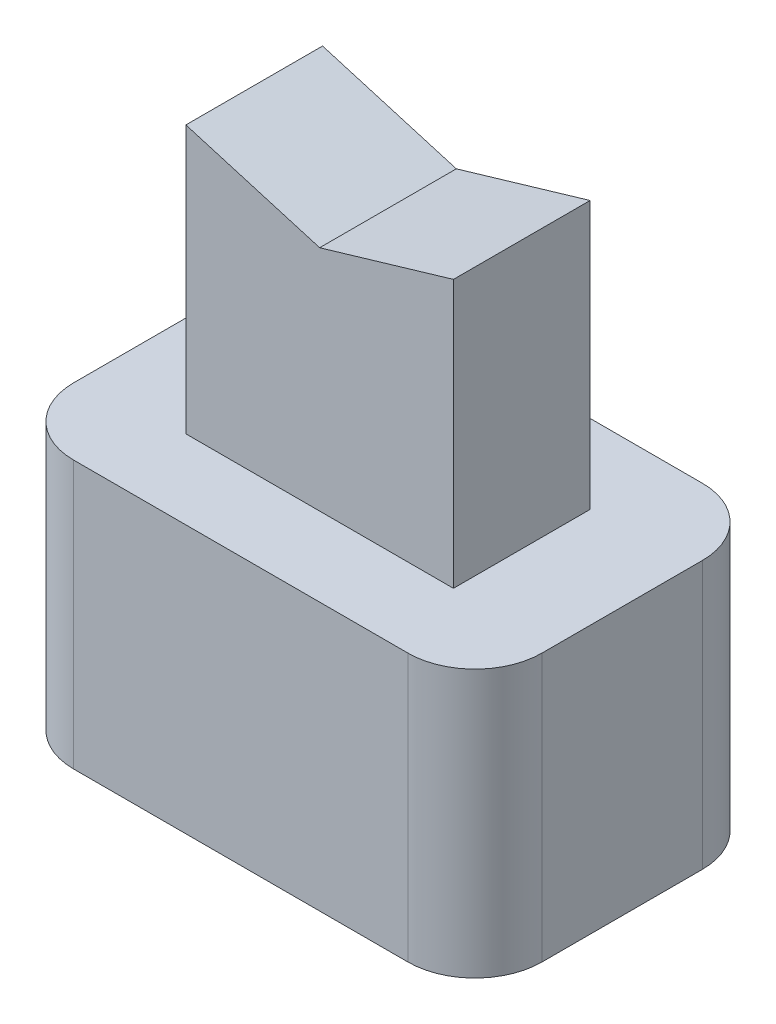
SolidWorks part; units mm, degrees
ref_plane "Alzado" through (0, 0, 0) normal (0, 0, 1) x (1, 0, 0)
ref_plane "Planta" through (0, 0, 0) normal (0, 1, 0) x (1, 0, 0)
ref_plane "Vista lateral" through (0, 0, 0) normal (1, 0, 0) x (0, 0, -1)
sketch "Croquis1" plane through (0, 0, 0) normal (0, 1, 0) x (1, 0, 0)
  line L1 (-3.5, -2.2) -> (3.5, -2.2)
  line L2 (-3.5, -2.2) -> (-3.5, 2.2)
  line L3 (-3.5, 2.2) -> (3.5, 2.2)
  line L4 (3.5, -2.2) -> (3.5, 2.2)
  line L5 (-3.5, -2.2) -> (3.5, 2.2) construction
  line L6 (-3.5, 2.2) -> (3.5, -2.2) construction
  point P0 (0, 0)
  dimension "D1" = 7
  dimension "D2" = 4.4
extrude "Saliente-Extruir1" add sketch "Croquis1" along normal blind 8
sketch "Croquis2" plane through (0, 8, 0) normal (0, 1, 0) x (1, 0, 0)
  line L1 (2, -1.0215) -> (-2, -1.0215)
  line L2 (2, -1.0215) -> (2, 1.0215)
  line L3 (2, 1.0215) -> (-2, 1.0215)
  line L4 (-2, -1.0215) -> (-2, 1.0215)
  line L5 (2, -1.0215) -> (-2, 1.0215) construction
  line L6 (2, 1.0215) -> (-2, -1.0215) construction
  point P0 (0, 0)
  dimension "D2" = 2.0431
  dimension "D3" = 4
extrude "Cortar-Extruir1" cut sketch "Croquis2" against normal blind 4 flip side to cut
fillet "Redondeo1" radius 1 4 edges at (3.5, 2, -2.2) (3.5, 2, 2.2) (-3.5, 2, 2.2) (-3.5, 2, -2.2)
sketch "Croquis3" plane through (0, 0, 1.0215) normal (0, 0, 1) x (1, 0, 0)
  line L0 (-2, 8) -> (0, 7.4098)
  line L1 (0, 7.4098) -> (2, 8)
extrude "Cortar-Extruir2" cut sketch "Croquis3" against normal through all and the other way through all
